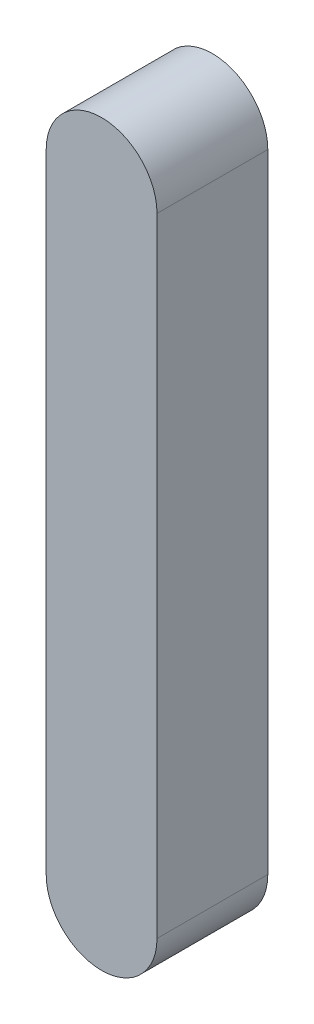
SolidWorks part; units mm, degrees
ref_plane "Front" through (0, 0, 0) normal (0, 0, 1) x (1, 0, 0)
ref_plane "Top" through (0, 0, 0) normal (0, 1, 0) x (1, 0, 0)
ref_plane "Right" through (0, 0, 0) normal (1, 0, 0) x (0, 0, -1)
sketch "Sketch1" plane through (0, 0, 0) normal (0, 0, 1) x (1, 0, 0)
  line L3 (74.2002, 56.8999) -> (74.2002, 22.8999)
  line L4 (80.2002, 56.8999) -> (80.2002, 22.8999)
  arc A0 (80.2002, 56.8999) -> (74.2002, 56.8999) centre (77.2002, 56.8999) ccw
  arc A1 (74.2002, 22.8999) -> (80.2002, 22.8999) centre (77.2002, 22.8999) ccw
  dimension "D1" = 34
extrude "Boss-Extrude1" add sketch "Sketch1" along normal blind 6 contours A0 L3 A1 L4
